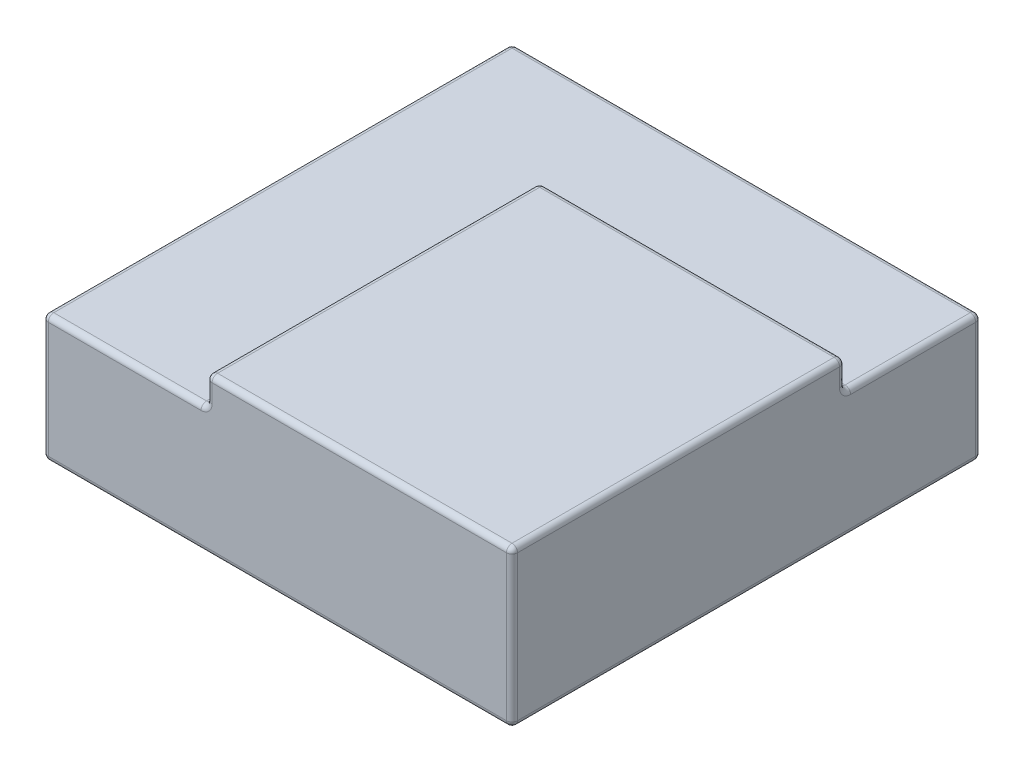
SolidWorks part; units mm, degrees
ref_plane "Front Plane" through (0, 0, 0) normal (0, 0, 1) x (1, 0, 0)
ref_plane "Top Plane" through (0, 0, 0) normal (0, 1, 0) x (1, 0, 0)
ref_plane "Right Plane" through (0, 0, 0) normal (1, 0, 0) x (0, 0, -1)
sketch "Sketch1" plane through (0, 0, 0) normal (0, 1, 0) x (1, 0, 0)
  line L1 (-32.385, -32.385) -> (32.385, -32.385)
  line L2 (-32.385, -32.385) -> (-32.385, 32.385)
  line L3 (-32.385, 32.385) -> (32.385, 32.385)
  line L4 (32.385, -32.385) -> (32.385, 32.385)
  line L5 (-32.385, -32.385) -> (32.385, 32.385) construction
  line L6 (-32.385, 32.385) -> (32.385, -32.385) construction
  point P0 (0, 0)
  dimension "D1" = 64.77
extrude "Boss-Extrude1" add sketch "Sketch1" along normal blind 21.59
sketch "Sketch2" plane through (0, 21.59, 0) normal (0, 1, 0) x (1, 0, 0)
  line L1 (32.385, -32.385) -> (-9.779, -32.385)
  line L2 (32.385, -32.385) -> (32.385, 13.589)
  line L3 (32.385, 13.589) -> (-9.779, 13.589)
  line L4 (-9.779, -32.385) -> (-9.779, 13.589)
  dimension "D1" = 42.164
  dimension "D2" = 45.974
extrude "Cut-Extrude1" cut sketch "Sketch2" against normal blind 4.064 flip side to cut
fillet "Fillet2" radius 0.762 21 edges at (-9.779, 19.558, -13.589) (32.385, 19.558, -13.589) (32.385, 0, 0) (32.385, 10.795, 32.385) (0, 0, 32.385) (-9.779, 19.558, 32.385) (-32.385, 8.763, 32.385) (-32.385, 0, 0) (-32.385, 8.763, -32.385) (0, 0, -32.385) (32.385, 8.763, -32.385) (11.303, 17.526, -13.589) (-9.779, 17.526, 9.398) (-21.082, 17.526, 32.385) (-32.385, 17.526, 0) (0, 17.526, -32.385) (32.385, 17.526, -22.987) (11.303, 21.59, -13.589) (32.385, 21.59, 9.398) (11.303, 21.59, 32.385) (-9.779, 21.59, 9.398)
